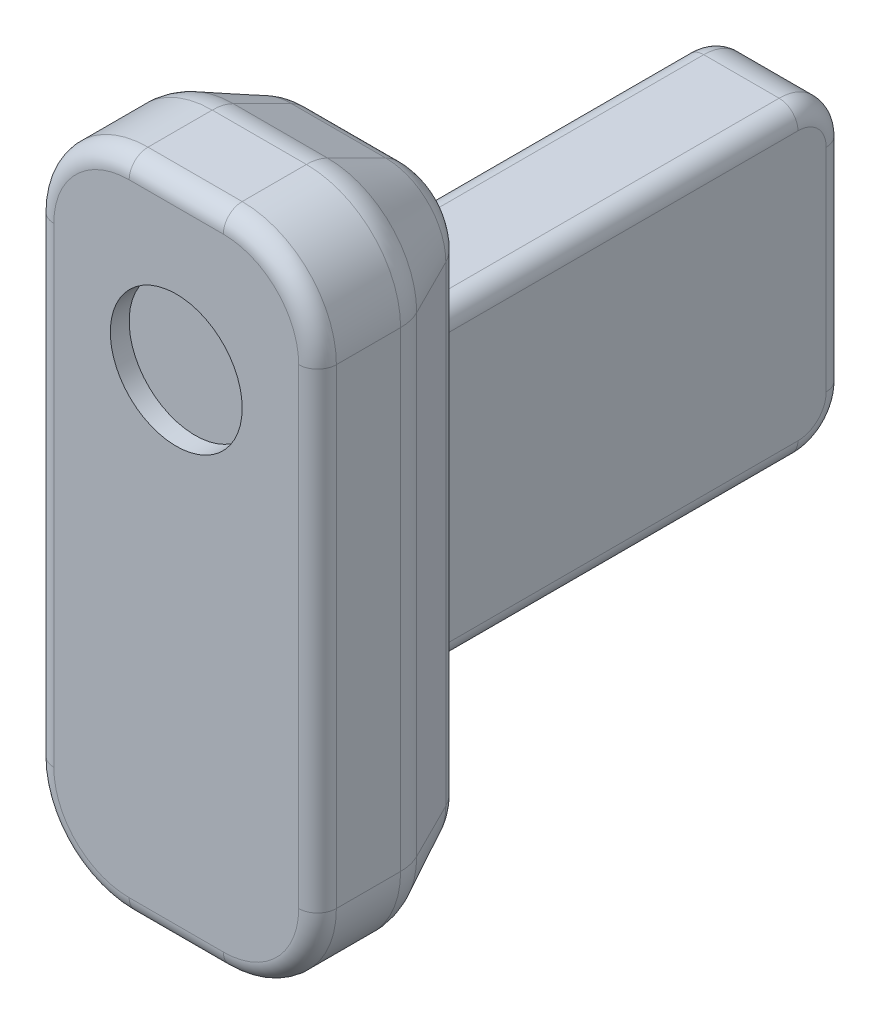
SolidWorks part; units mm, degrees
ref_plane "Front Plane" through (0, 0, 0) normal (0, 0, 1) x (1, 0, 0)
ref_plane "Top Plane" through (0, 0, 0) normal (0, 1, 0) x (1, 0, 0)
ref_plane "Right Plane" through (0, 0, 0) normal (1, 0, 0) x (0, 0, -1)
sketch "Sketch1" plane through (0, 0, 0) normal (0, 0, 1) x (1, 0, 0)
  line L1 (42.3673, -46.3138) -> (72.3673, -46.3138)
  line L2 (42.3673, -46.3138) -> (42.3673, -116.3138)
  line L3 (42.3673, -116.3138) -> (72.3673, -116.3138)
  line L4 (72.3673, -46.3138) -> (72.3673, -116.3138)
  dimension "D1" = 30
  dimension "D2" = 70
extrude "Boss-Extrude1" add sketch "Sketch1" against normal blind 20
fillet "Fillet1" radius 10 4 edges at (42.3673, -46.3138, -10) (72.3673, -46.3138, -10) (42.3673, -116.3138, -10) (72.3673, -116.3138, -10)
fillet "Fillet2" radius 2 8 edges at (69.4383, -113.3848, 0) (57.3673, -116.3138, 0) (45.2962, -113.3848, 0) (42.3673, -81.3138, 0) (45.2962, -49.2427, 0) (57.3673, -46.3138, 0) (69.4383, -49.2427, 0) (72.3673, -81.3138, 0)
chamfer "Chamfer1" distance 5 distance2 10 8 edges at (42.3673, -81.3138, -20) (45.2962, -113.3848, -20) (45.2962, -49.2427, -20) (57.3673, -116.3138, -20) (57.3673, -46.3138, -20) (69.4383, -113.3848, -20) (69.4383, -49.2427, -20) (72.3673, -81.3138, -20)
fillet "Fillet3" radius 5 16 edges at (65.9028, -52.7782, -20) (57.3673, -51.3138, -20) (48.8317, -52.7782, -20) (47.3673, -81.3138, -20) (48.8317, -109.8493, -20) (57.3673, -111.3138, -20) (65.9028, -109.8493, -20) (69.4383, -113.3848, -10) (57.3673, -116.3138, -10) (45.2962, -113.3848, -10) (42.3673, -81.3138, -10) (45.2962, -49.2427, -10) (57.3673, -46.3138, -10) (69.4383, -49.2427, -10) (67.3673, -81.3138, -20) (72.3673, -81.3138, -10)
sketch "Sketch2" plane through (0, 0, -20) normal (0, 0, -1) x (-1, 0, 0)
  line L0 (-64.2771, -81.3138) -> (-50.4574, -81.3138) construction
  line L1 (-64.2771, -56.3138) -> (-64.2771, -106.3138) construction
  line L2 (-50.4574, -106.3138) -> (-50.4574, -56.3138) construction
  line L3 (-57.3673, -108.2236) -> (-57.3673, -54.4039) construction
  line L4 (-62.3673, -108.2236) -> (-52.3673, -108.2236) construction
  line L5 (-52.3673, -54.4039) -> (-62.3673, -54.4039) construction
  line L7 (-63.3673, -98.8138) -> (-51.3673, -98.8138)
  line L8 (-63.3673, -98.8138) -> (-63.3673, -66.3138)
  line L9 (-63.3673, -66.3138) -> (-51.3673, -66.3138)
  line L10 (-51.3673, -98.8138) -> (-51.3673, -66.3138)
  dimension "D3" = 32.5
extrude "Boss-Extrude2" add sketch "Sketch2" along normal blind 45
fillet "Fillet4" radius 5 2 edges at (57.3673, -66.3138, -65) (57.3673, -98.8138, -65)
sketch "Sketch3" plane through (0, 0, 0) normal (0, 0, 1) x (1, 0, 0)
  line L0 (57.3673, -48.3138) -> (57.3673, -114.3138) construction
  line L1 (62.3673, -48.3138) -> (52.3673, -48.3138) construction
  line L2 (52.3673, -114.3138) -> (62.3673, -114.3138) construction
  line L3 (52.3673, -46.3138) -> (62.3673, -46.3138) construction
  circle A0 centre (57.3673, -63.3138) radius 7
  dimension "D1" = 17
extrude "Cut-Extrude1" cut sketch "Sketch3" against normal blind 2
fillet "Fillet5" radius 2 10 edges at (51.3673, -66.3138, -40) (51.3673, -67.7782, -63.5355) (51.3673, -82.5638, -65) (51.3673, -97.3493, -63.5355) (63.3673, -66.3138, -40) (63.3673, -67.7782, -63.5355) (63.3673, -82.5638, -65) (63.3673, -97.3493, -63.5355) (51.3673, -98.8138, -40) (63.3673, -98.8138, -40)
